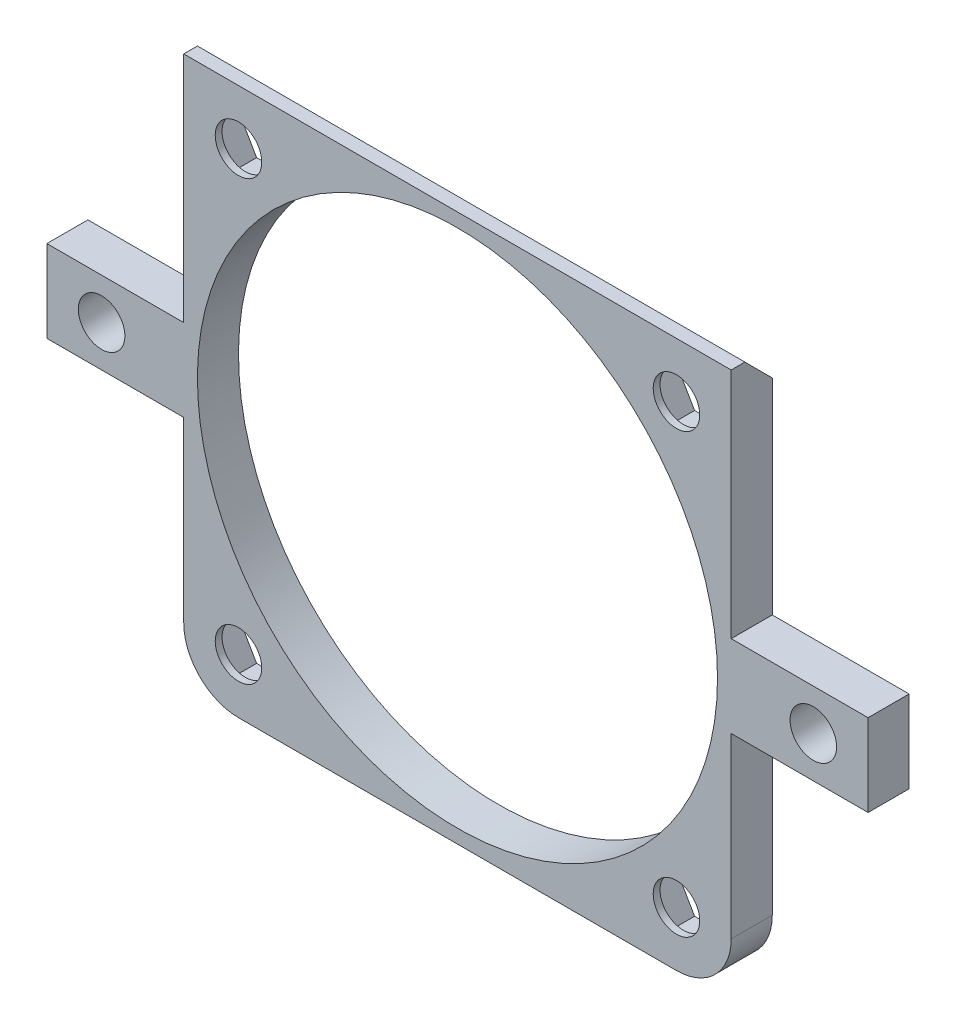
SolidWorks part; units mm, degrees
ref_plane "Alzado" through (0, 0, 0) normal (0, 0, 1) x (1, 0, 0)
ref_plane "Planta" through (0, 0, 0) normal (0, 1, 0) x (1, 0, 0)
ref_plane "Vista lateral" through (0, 0, 0) normal (1, 0, 0) x (0, 0, -1)
sketch "Croquis1" plane through (0, 0, 0) normal (0, 0, 1) x (1, 0, 0)
  line L0 (-30, 3) -> (-30, -3)
  line L1 (-30, -3) -> (-20, -3)
  line L2 (-20, -3) -> (-20, -20)
  line L3 (-20, -20) -> (20, -20)
  line L4 (20, -20) -> (20, -3)
  line L5 (20, -3) -> (30, -3)
  line L6 (30, -3) -> (30, 3)
  line L7 (30, 3) -> (20, 3)
  line L8 (20, 3) -> (20, 20)
  line L9 (20, 20) -> (-20, 20)
  line L10 (-20, 20) -> (-20, 3)
  line L11 (-20, 3) -> (-30, 3)
  line L12 (-20, 20) -> (20, -20) construction
  line L13 (-20, -20) -> (20, 20) construction
  circle A0 centre (0, 0) radius 19
  circle A1 centre (-26, 0) radius 1.7
  circle A2 centre (26, 0) radius 1.7
  circle A3 centre (16, 16) radius 1.7
  circle A4 centre (-16, 16) radius 1.7
  circle A5 centre (-16, -16) radius 1.7
  circle A6 centre (16, -16) radius 1.7
  point P16 (0, 20)
  point P17 (-30, 0)
  point P29 (-16.9364, 14.8341)
  point P30 (0, 0)
  dimension "D5" = 38
  dimension "D6" = 3.4
  dimension "D1" = 40
  dimension "D2" = 40
  dimension "D3" = 10
  dimension "D4" = 6
  dimension "D7" = 32
  dimension "D8" = 32
  dimension "D9" = 26
  dimension "D10" = 26
extrude "Saliente-Extruir1" add sketch "Croquis1" along normal blind 3
sketch "Croquis2" plane through (-20, 0, 0) normal (-1, 0, 0) x (0, 0, 1)
  line L0 (2, 20) -> (0, 20)
  line L1 (0, 20) -> (0, 18)
  line L2 (0, 18) -> (2, 20)
  point P2 (0, 24.0076)
  point P5 (0, 0)
  dimension "D1" = 2
  dimension "D2" = 45
extrude "Cortar-Extruir1" cut sketch "Croquis2" against normal up to surface (40 mm away) up to face at (20, 11.5, 1.5)
fillet "Redondeo1" radius 4 2 edges at (20, -20, 1.5) (-20, -20, 1.5)
sketch "Croquis3" plane through (0, 0, 0) normal (0, 0, -1) x (-1, 0, 0)
  line L0 (-30, 3) -> (-20, 3) construction
  line L1 (-12.65, 16) -> (-14.325, 18.9012)
  line L2 (-14.325, 18.9012) -> (-17.675, 18.9012)
  line L3 (-17.675, 18.9012) -> (-19.35, 16)
  line L4 (-19.35, 16) -> (-17.675, 13.0988)
  line L5 (-17.675, 13.0988) -> (-14.325, 13.0988)
  line L6 (-14.325, 13.0988) -> (-12.65, 16)
  line L7 (-12.65, -16) -> (-14.325, -13.0988)
  line L8 (-14.325, -13.0988) -> (-17.675, -13.0988)
  line L9 (-17.675, -13.0988) -> (-19.35, -16)
  line L10 (-19.35, -16) -> (-17.675, -18.9012)
  line L11 (-17.675, -18.9012) -> (-14.325, -18.9012)
  line L12 (-14.325, -18.9012) -> (-12.65, -16)
  line L13 (19.35, -16) -> (17.675, -13.0988)
  line L14 (17.675, -13.0988) -> (14.325, -13.0988)
  line L15 (14.325, -13.0988) -> (12.65, -16)
  line L16 (12.65, -16) -> (14.325, -18.9012)
  line L17 (14.325, -18.9012) -> (17.675, -18.9012)
  line L18 (17.675, -18.9012) -> (19.35, -16)
  line L19 (19.35, 16) -> (17.675, 18.9012)
  line L20 (17.675, 18.9012) -> (14.325, 18.9012)
  line L21 (14.325, 18.9012) -> (12.65, 16)
  line L22 (12.65, 16) -> (14.325, 13.0988)
  line L23 (14.325, 13.0988) -> (17.675, 13.0988)
  line L24 (17.675, 13.0988) -> (19.35, 16)
  circle A0 centre (-16, 16) radius 3.35 construction
  circle A1 centre (-16, -16) radius 3.35 construction
  circle A2 centre (16, -16) radius 3.35 construction
  circle A3 centre (16, 16) radius 3.35 construction
  dimension "D1" = 6.7
extrude "Cortar-Extruir2" cut sketch "Croquis3" against normal blind 2.5
